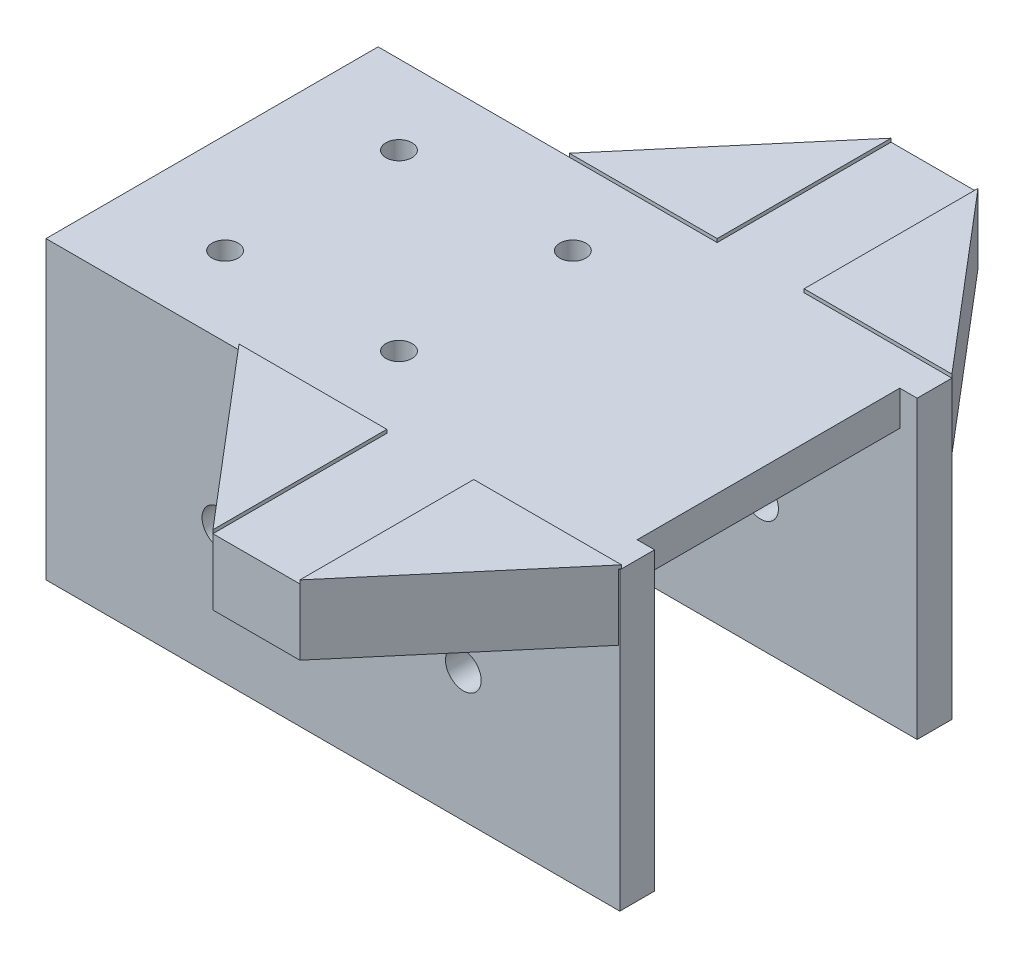
SolidWorks part; units mm, degrees
ref_plane "Ebene vorne" through (0, 0, 0) normal (0, 0, 1) x (1, 0, 0)
ref_plane "Ebene oben" through (0, 0, 0) normal (0, 1, 0) x (1, 0, 0)
ref_plane "Ebene rechts" through (0, 0, 0) normal (1, 0, 0) x (0, 0, -1)
sketch "Skizze1" plane through (0, 0, 0) normal (0, 1, 0) x (1, 0, 0)
  line L0 (-22.5, 10) -> (-2.5, 10) construction
  line L1 (30, -15.1) -> (-30, -15.1)
  line L2 (30, -15.1) -> (30, 15.1)
  line L3 (30, 15.1) -> (-30, 15.1)
  line L4 (-30, -15.1) -> (-30, 15.1)
  line L5 (30, -15.1) -> (-30, 15.1) construction
  line L6 (30, 15.1) -> (-30, -15.1) construction
  line L7 (-2.5, 10) -> (-2.5, -10) construction
  line L8 (-2.5, -10) -> (-22.5, -10) construction
  line L9 (-22.5, -10) -> (-22.5, 10) construction
  line L10 (-22.5, 0) -> (-2.5, 0) construction
  line L11 (0, 0) -> (11.6154, 0) construction
  circle A0 centre (-22.5, 10) radius 1.5
  circle A1 centre (-22.5, -10) radius 1.5
  circle A2 centre (-2.5, 10) radius 1.5
  circle A3 centre (-2.5, -10) radius 1.5
  point P0 (0, 0)
  dimension "D3" = 3
  dimension "D6" = 15.1
  dimension "D1" = 60
  dimension "D2" = 30.2
  dimension "D4" = 20
  dimension "D5" = 20
  dimension "D7" = 7.5
extrude "Aufsatz-Linear austragen1" add sketch "Skizze1" along normal blind 4
sketch "Skizze2" plane through (0, 4, 0) normal (0, 1, 0) x (1, 0, 0)
  line L0 (30, 15.1) -> (-30, 15.1) construction
  line L1 (32, -17.1) -> (-32, -17.1)
  line L2 (30, -15.1) -> (30, 15.1) construction
  line L3 (32, 17.1) -> (-32, 17.1)
  line L4 (-32, -17.1) -> (-32, 17.1)
  line L5 (32, -17.1) -> (-32, 17.1) construction
  line L6 (32, 17.1) -> (-32, -17.1) construction
  line L7 (-30, 15.1) -> (-30, -15.1) construction
  point P0 (0, 0)
  point P12 (32, 17.1)
  point P13 (32, 17.1)
  dimension "D1" = 2
  dimension "D2" = 2
  dimension "D3" = 2
extrude "Linear-Austragen-Dünn1" add sketch "Skizze2" against normal blind 34 thin thin type mid plane wall 4
hole_wizard "Ø4.1 (4.1) Durchmesser Bohrung1" positions "3D-Skizze1" profile "Skizze3" hole size "Ø4.1" standard "DIN" end condition through all
sketch3d "3D-Skizze1"
  line L0 (-34, -30, 0) -> (-34, -16.1713, 0) construction
  line L1 (-34, -30, -19.1) -> (-34, -30, 19.1) construction
  line L3 (-34, -15, -19.1) -> (32, -15, -19.1) construction
  line L4 (-34, -30, -19.1) -> (-34, 4, -19.1) construction
  line L5 (32, -30, -19.1) -> (32, 4, -19.1) construction
  line L7 (32, -30, -19.1) -> (-34, -30, -19.1) construction
  point P0 (-14, -14.8082, -19.1)
  point P2 (13.9993, -15, -19.1)
  point P4 (-34, -15, 0)
  point P20 (-15.6339, -20.0544, -19.1)
  point P21 (12.0334, -20.0544, -19.1)
  point P24 (-14, -15, -19.1)
  point P25 (13.9993, -15, -19.1)
  dimension "D1" = 28
  dimension "D2" = 20
  dimension "D3" = 15
  dimension "D4" = 15
sketch "Skizze3" plane through (-14, -14.8082, -19.1) normal (1, 0, 0) x (0, 1, 0)
  line L0 (0, 0) -> (0, 38.2)
  line L1 (0, 38.2) -> (2.05, 38.2)
  line L2 (2.05, 38.2) -> (2.05, 0)
  line L5 (2.05, 0) -> (0, 0)
  line L11 (0, -6.35) -> (0, 107.95) construction
  dimension "Bohrerdurchmesser" = 4.1
  dimension "Bohrungstiefe" = 38.2
sketch "Skizze4" plane through (0, 0, -19.1) normal (0, 0, -1) x (-1, 0, 0)
  line L0 (-32, 4) -> (34, 4) construction
  line L1 (-15, 4) -> (-5, 4)
  line L2 (-15, 4) -> (-15, -3.6)
  line L3 (-15, -3.6) -> (-5, -3.6)
  line L4 (-5, 4) -> (-5, -3.6)
  line L5 (-32, -30) -> (-32, 4) construction
  dimension "D1" = 7.6
  dimension "D2" = 17
  dimension "D3" = 10
extrude "Aufsatz-Linear austragen3" add sketch "Skizze4" along normal blind 20
sketch "Skizze5" plane through (15, 0, 0) normal (1, 0, 0) x (0, 0, -1)
  line L0 (39.1, -3.6) -> (19.1, -3.6) construction
  line L1 (38.1, -3.6) -> (37.1, -3.6)
  line L2 (38.1, -3.6) -> (38.1, -1.6)
  line L3 (38.1, -1.6) -> (37.1, -1.6)
  line L4 (37.1, -3.6) -> (37.1, -1.6)
  line L5 (39.1, 4) -> (39.1, -3.6) construction
  line L6 (36.1, -3.6) -> (36.1, -1.6)
  line L7 (36.1, -1.6) -> (35.1, -1.6)
  line L8 (35.1, -3.6) -> (35.1, -1.6)
  line L9 (36.1, -3.6) -> (35.1, -3.6)
  line L10 (34.1, -3.6) -> (34.1, -1.6)
  line L11 (34.1, -1.6) -> (33.1, -1.6)
  line L12 (33.1, -3.6) -> (33.1, -1.6)
  line L13 (34.1, -3.6) -> (33.1, -3.6)
  line L14 (32.1, -3.6) -> (32.1, -1.6)
  line L15 (32.1, -1.6) -> (31.1, -1.6)
  line L16 (31.1, -3.6) -> (31.1, -1.6)
  line L17 (32.1, -3.6) -> (31.1, -3.6)
  line L18 (30.1, -3.6) -> (30.1, -1.6)
  line L19 (30.1, -1.6) -> (29.1, -1.6)
  line L20 (29.1, -3.6) -> (29.1, -1.6)
  line L21 (30.1, -3.6) -> (29.1, -3.6)
  line L22 (28.1, -3.6) -> (28.1, -1.6)
  line L23 (28.1, -1.6) -> (27.1, -1.6)
  line L24 (27.1, -3.6) -> (27.1, -1.6)
  line L25 (28.1, -3.6) -> (27.1, -3.6)
  line L26 (26.1, -3.6) -> (26.1, -1.6)
  line L27 (26.1, -1.6) -> (25.1, -1.6)
  line L28 (25.1, -3.6) -> (25.1, -1.6)
  line L29 (26.1, -3.6) -> (25.1, -3.6)
  line L30 (24.1, -3.6) -> (24.1, -1.6)
  line L31 (24.1, -1.6) -> (23.1, -1.6)
  line L32 (23.1, -3.6) -> (23.1, -1.6)
  line L33 (24.1, -3.6) -> (23.1, -3.6)
  line L34 (22.1, -3.6) -> (22.1, -1.6)
  line L35 (22.1, -1.6) -> (21.1, -1.6)
  line L36 (21.1, -3.6) -> (21.1, -1.6)
  line L37 (22.1, -3.6) -> (21.1, -3.6)
  dimension "D1" = 2
  dimension "D2" = 1
  dimension "D3" = 1
  dimension "D4" = 9
extrude "Schnitt-Linear austragen1" cut sketch "Skizze5" against normal blind 20
sketch "Skizze6" plane through (0, -3.6, 0) normal (0, -1, 0) x (1, 0, 0)
  line L0 (15, -39.1) -> (32, -19.1)
  line L1 (32, -19.1) -> (15, -19.1)
  line L2 (15, -19.1) -> (15, -39.1)
  line L3 (5, -39.1) -> (5, -19.1)
  line L4 (5, -19.1) -> (-12, -19.1)
  line L5 (32, -19.1) -> (-34, -19.1) construction
  line L6 (-12, -19.1) -> (5, -39.1)
  dimension "D1" = 17
extrude "Aufsatz-Linear austragen4" add sketch "Skizze6" against normal blind 8
ref_plane "Ebene1" through (0, 0, -0.1) normal (0, 0, 1) x (1, 0, 0)
mirror "Spiegeln1" about plane through (0, 0, -0.1) normal (0, 0, 1) of "Aufsatz-Linear austragen4", "Schnitt-Linear austragen1", "Aufsatz-Linear austragen3"
